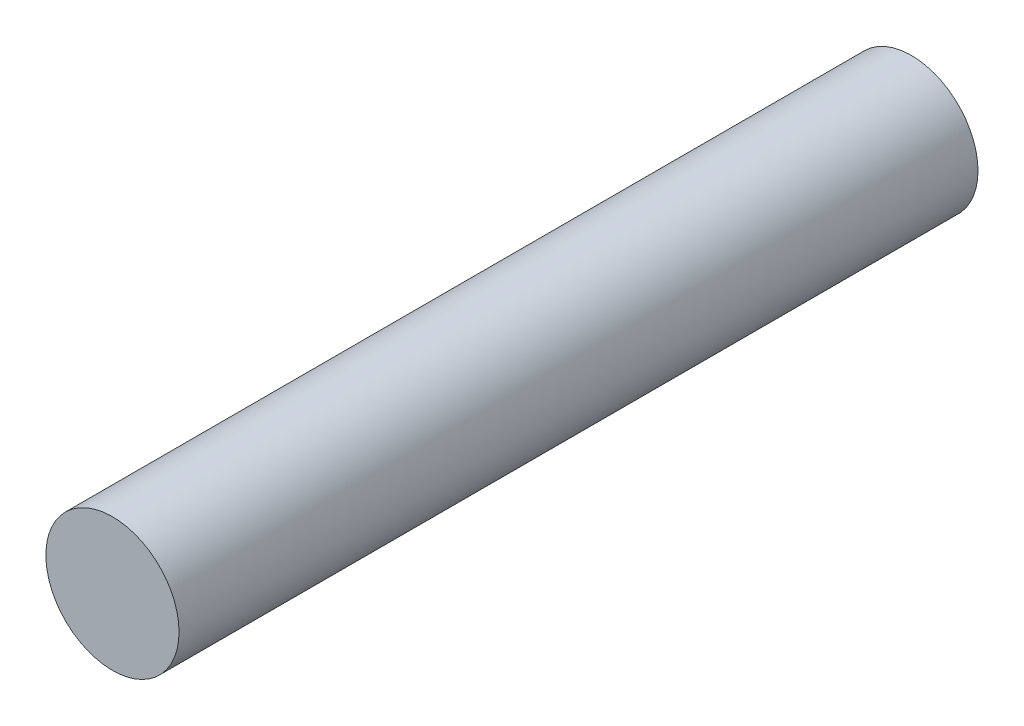
SolidWorks part; units mm, degrees
ref_plane "Plan de face" through (0, 0, 0) normal (0, 0, 1) x (1, 0, 0)
ref_plane "Plan de dessus" through (0, 0, 0) normal (0, 1, 0) x (1, 0, 0)
ref_plane "Plan de droite" through (0, 0, 0) normal (1, 0, 0) x (0, 0, -1)
sketch "Esquisse1" plane through (0, 0, 0) normal (0, 0, 1) x (1, 0, 0)
  circle A0 centre (0, 0) radius 2.5
extrude "Boss.-Extru.1" add sketch "Esquisse1" along normal blind 30
